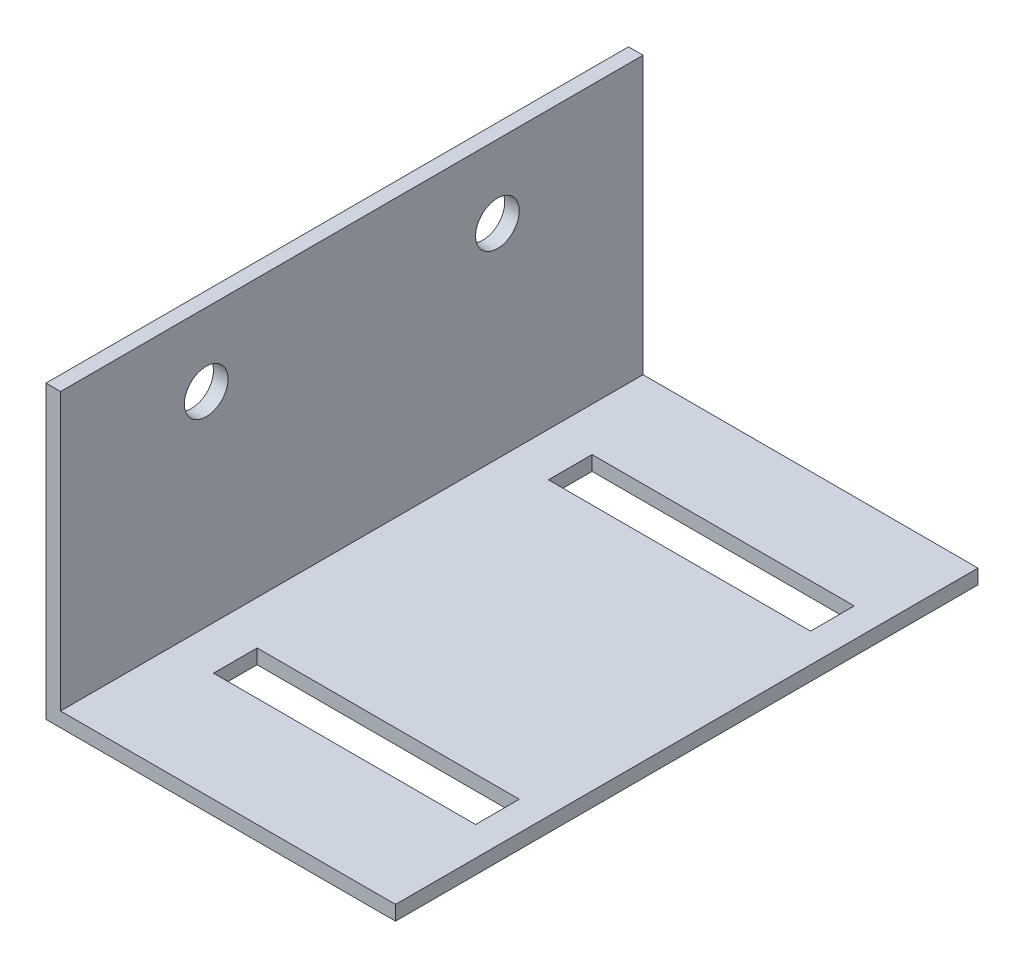
SolidWorks part; units mm, degrees
ref_plane "Front Plane" through (0, 0, 0) normal (0, 0, 1) x (1, 0, 0)
ref_plane "Top Plane" through (0, 0, 0) normal (0, 1, 0) x (1, 0, 0)
ref_plane "Right Plane" through (0, 0, 0) normal (1, 0, 0) x (0, 0, -1)
sketch "Sketch1" plane through (0, 0, 0) normal (0, 0, 1) x (1, 0, 0)
  line L0 (0, 0) -> (24, 0)
  line L1 (24, 0) -> (24, 1)
  line L2 (24, 1) -> (1, 1)
  line L3 (1, 1) -> (1, 20)
  line L4 (1, 20) -> (0, 20)
  line L5 (0, 20) -> (0, 0)
  dimension "D1" = 23
  dimension "D2" = 1
  dimension "D3" = 19
  dimension "D4" = 1
  dimension "D5" = 20
  dimension "D6" = 24
extrude "Boss-Extrude1" add sketch "Sketch1" along normal blind 40
sketch "Sketch2" plane through (0, 1, 0) normal (0, 1, 0) x (1, 0, 0)
  line L0 (24, -40) -> (24, 0) construction
  line L1 (4, -6.5) -> (22, -6.5)
  line L2 (4, -6.5) -> (4, -9.5)
  line L3 (4, -9.5) -> (22, -9.5)
  line L4 (22, -6.5) -> (22, -9.5)
  line L5 (24, 0) -> (1, 0) construction
  line L6 (4, -32.5) -> (22, -32.5)
  line L7 (4, -32.5) -> (4, -29.5)
  line L8 (4, -29.5) -> (22, -29.5)
  line L9 (22, -32.5) -> (22, -29.5)
  point P10 (4, -8)
  point P11 (4, -31)
  dimension "D1" = 3
  dimension "D2" = 18
  dimension "D3" = 2
  dimension "D4" = 3
  dimension "D5" = 18
  dimension "D6" = 23
  dimension "D7" = 2
  dimension "D8" = 8
extrude "Cut-Extrude1" cut sketch "Sketch2" against normal blind 10
sketch "Sketch3" plane through (0, 0, 0) normal (-1, 0, 0) x (0, 0, 1)
  line L0 (0, 20) -> (0, 0) construction
  line L1 (40, 20) -> (40, 0) construction
  line L2 (40, 0) -> (0, 0) construction
  circle A0 centre (30, 15) radius 1.5
  circle A1 centre (10, 15) radius 1.5
  dimension "D1" = 3
  dimension "D2" = 3
  dimension "D4" = 10
  dimension "D5" = 15
  dimension "D6" = 3
  dimension "D7" = 15
  dimension "D3" = 10
extrude "Cut-Extrude2" cut sketch "Sketch3" against normal blind 10
